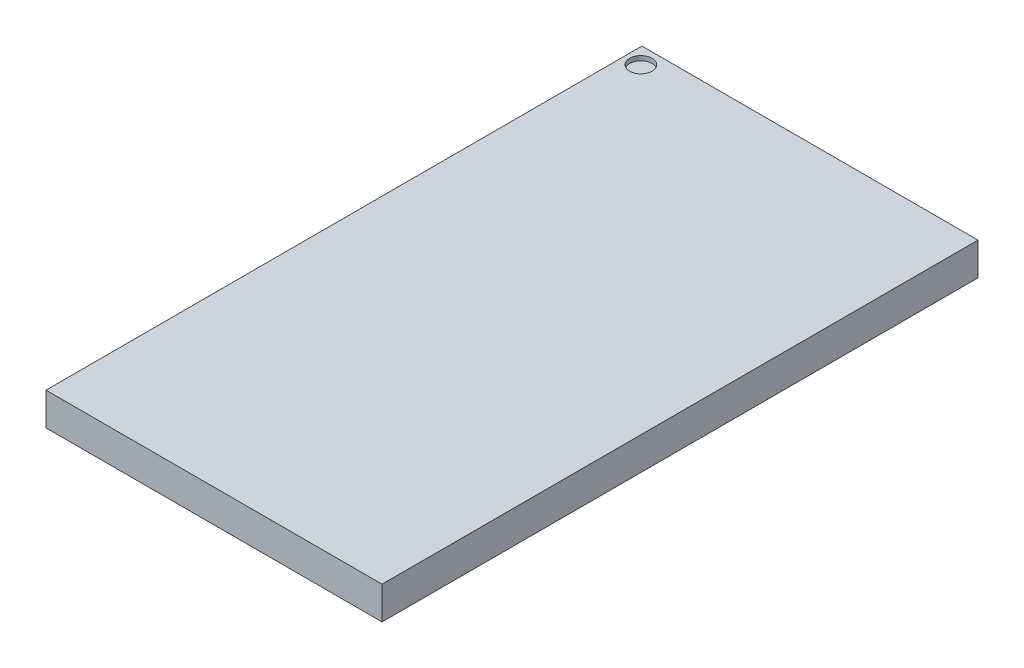
SolidWorks part; units mm, degrees
ref_plane "Front Plane" through (0, 0, 0) normal (0, 0, 1) x (1, 0, 0)
ref_plane "Top Plane" through (0, 0, 0) normal (0, 1, 0) x (1, 0, 0)
ref_plane "Right Plane" through (0, 0, 0) normal (1, 0, 0) x (0, 0, -1)
sketch "Sketch1" plane through (0, 0, 0) normal (0, 1, 0) x (1, 0, 0)
  line L1 (3.75, -6.65) -> (-3.75, -6.65)
  line L2 (3.75, -6.65) -> (3.75, 6.65)
  line L3 (3.75, 6.65) -> (-3.75, 6.65)
  line L4 (-3.75, -6.65) -> (-3.75, 6.65)
  line L5 (3.75, -6.65) -> (-3.75, 6.65) construction
  line L6 (3.75, 6.65) -> (-3.75, -6.65) construction
  point P0 (0, 0)
extrude "Boss-Extrude1" add sketch "Sketch1" along normal blind 0.73
sketch "Sketch2" plane through (0, 0.73, 0) normal (0, 1, 0) x (1, 0, 0)
  circle A0 centre (-3.401, 6.2774) radius 0.25
  point P2 (-4.8053, 5.4314)
  point P3 (-3.401, 6.2774)
  point P4 (0, 0)
extrude "Cut-Extrude1" cut sketch "Sketch2" against normal blind 0.1
sketch "Sketch3" plane through (0, 0, 0) normal (0, -1, 0) x (1, 0, 0)
  line L0 (-3.75, 6.65) -> (-3.195, 6.65) construction
  line L1 (-3.75, 6.65) -> (3.75, 6.65) construction
  line L2 (-3.75, 6.65) -> (-3.75, 6) construction
  line L3 (-3.75, -6.65) -> (-3.75, 6.65) construction
  line L4 (0, -6.65) -> (0, 6.65) construction
  line L5 (3.75, -6.65) -> (-3.75, -6.65) construction
  line L6 (3.75, 6.65) -> (3.75, 6) construction
  line L7 (3.75, 6.65) -> (3.195, 6.65) construction
  circle A0 centre (-3.195, 6) radius 0.2
  circle A1 centre (-2.395, 6) radius 0.2
  circle A2 centre (-1.595, 6) radius 0.2
  circle A3 centre (-2.395, 5.2) radius 0.2
  circle A4 centre (-1.595, 5.2) radius 0.2
  circle A5 centre (-2.395, 4.4) radius 0.2
  circle A6 centre (-1.595, 4.4) radius 0.2
  circle A7 centre (-2.395, 3.6) radius 0.2
  circle A8 centre (-1.595, 3.6) radius 0.2
  circle A9 centre (-2.395, 2.8) radius 0.2
  circle A10 centre (-1.595, 2.8) radius 0.2
  circle A11 centre (-2.395, 2) radius 0.2
  circle A12 centre (-1.595, 2) radius 0.2
  circle A13 centre (-2.395, 1.2) radius 0.2
  circle A14 centre (-1.595, 1.2) radius 0.2
  circle A15 centre (-2.395, 0.4) radius 0.2
  circle A16 centre (-1.595, 0.4) radius 0.2
  circle A17 centre (-2.395, -0.4) radius 0.2
  circle A18 centre (-1.595, -0.4) radius 0.2
  circle A19 centre (-2.395, -1.2) radius 0.2
  circle A20 centre (-1.595, -1.2) radius 0.2
  circle A21 centre (-2.395, -2) radius 0.2
  circle A22 centre (-1.595, -2) radius 0.2
  circle A23 centre (-2.395, -2.8) radius 0.2
  circle A24 centre (-1.595, -2.8) radius 0.2
  circle A25 centre (-2.395, -3.6) radius 0.2
  circle A26 centre (-1.595, -3.6) radius 0.2
  circle A27 centre (-2.395, -4.4) radius 0.2
  circle A28 centre (-1.595, -4.4) radius 0.2
  circle A29 centre (-2.395, -5.2) radius 0.2
  circle A30 centre (-1.595, -5.2) radius 0.2
  circle A31 centre (-2.395, -6) radius 0.2
  circle A32 centre (-1.595, -6) radius 0.2
  circle A33 centre (-3.195, 5.2) radius 0.2
  circle A34 centre (-3.195, 4.4) radius 0.2
  circle A35 centre (-3.195, 3.6) radius 0.2
  circle A36 centre (-3.195, 2.8) radius 0.2
  circle A37 centre (-3.195, 2) radius 0.2
  circle A38 centre (-3.195, 1.2) radius 0.2
  circle A39 centre (-3.195, 0.4) radius 0.2
  circle A40 centre (-3.195, -0.4) radius 0.2
  circle A41 centre (-3.195, -1.2) radius 0.2
  circle A42 centre (-3.195, -2) radius 0.2
  circle A43 centre (-3.195, -2.8) radius 0.2
  circle A44 centre (-3.195, -3.6) radius 0.2
  circle A45 centre (-3.195, -4.4) radius 0.2
  circle A46 centre (-3.195, -5.2) radius 0.2
  circle A47 centre (-3.195, -6) radius 0.2
  circle A48 centre (3.195, -6) radius 0.2
  circle A49 centre (3.195, -5.2) radius 0.2
  circle A50 centre (3.195, -4.4) radius 0.2
  circle A51 centre (3.195, -3.6) radius 0.2
  circle A52 centre (3.195, -2.8) radius 0.2
  circle A53 centre (3.195, -2) radius 0.2
  circle A54 centre (3.195, -1.2) radius 0.2
  circle A55 centre (3.195, -0.4) radius 0.2
  circle A56 centre (3.195, 0.4) radius 0.2
  circle A57 centre (3.195, 1.2) radius 0.2
  circle A58 centre (3.195, 2) radius 0.2
  circle A59 centre (3.195, 2.8) radius 0.2
  circle A60 centre (3.195, 3.6) radius 0.2
  circle A61 centre (3.195, 4.4) radius 0.2
  circle A62 centre (3.195, 5.2) radius 0.2
  circle A63 centre (1.595, -6) radius 0.2
  circle A64 centre (2.395, -6) radius 0.2
  circle A65 centre (1.595, -5.2) radius 0.2
  circle A66 centre (2.395, -5.2) radius 0.2
  circle A67 centre (1.595, -4.4) radius 0.2
  circle A68 centre (2.395, -4.4) radius 0.2
  circle A69 centre (1.595, -3.6) radius 0.2
  circle A70 centre (2.395, -3.6) radius 0.2
  circle A71 centre (1.595, -2.8) radius 0.2
  circle A72 centre (2.395, -2.8) radius 0.2
  circle A73 centre (1.595, -2) radius 0.2
  circle A74 centre (2.395, -2) radius 0.2
  circle A75 centre (1.595, -1.2) radius 0.2
  circle A76 centre (2.395, -1.2) radius 0.2
  circle A77 centre (1.595, -0.4) radius 0.2
  circle A78 centre (2.395, -0.4) radius 0.2
  circle A79 centre (1.595, 0.4) radius 0.2
  circle A80 centre (2.395, 0.4) radius 0.2
  circle A81 centre (1.595, 1.2) radius 0.2
  circle A82 centre (2.395, 1.2) radius 0.2
  circle A83 centre (1.595, 2) radius 0.2
  circle A84 centre (2.395, 2) radius 0.2
  circle A85 centre (1.595, 2.8) radius 0.2
  circle A86 centre (2.395, 2.8) radius 0.2
  circle A87 centre (1.595, 3.6) radius 0.2
  circle A88 centre (2.395, 3.6) radius 0.2
  circle A89 centre (1.595, 4.4) radius 0.2
  circle A90 centre (2.395, 4.4) radius 0.2
  circle A91 centre (1.595, 5.2) radius 0.2
  circle A92 centre (2.395, 5.2) radius 0.2
  circle A93 centre (1.595, 6) radius 0.2
  circle A94 centre (2.395, 6) radius 0.2
  circle A95 centre (3.195, 6) radius 0.2
  dimension "D1" = 3
  dimension "D2" = 16
extrude "Boss-Extrude2" add sketch "Sketch3" along normal blind 0.3
fillet "Fillet1" radius 0.15 96 edges at (3.195, -0.3, 6.2) (2.395, -0.3, 6.2) (1.595, -0.3, 6.2) (2.395, -0.3, 5.4) (1.595, -0.3, 5.4) (2.395, -0.3, 4.6) (1.595, -0.3, 4.6) (2.395, -0.3, 3.8) (1.595, -0.3, 3.8) (2.395, -0.3, 3) (1.595, -0.3, 3) (2.395, -0.3, 2.2) (1.595, -0.3, 2.2) (2.395, -0.3, 1.4) (1.595, -0.3, 1.4) (2.395, -0.3, 0.6) (1.595, -0.3, 0.6) (2.395, -0.3, -0.2) (1.595, -0.3, -0.2) (2.395, -0.3, -1) (1.595, -0.3, -1) (2.395, -0.3, -1.8) (1.595, -0.3, -1.8) (2.395, -0.3, -2.6) (1.595, -0.3, -2.6) (2.395, -0.3, -3.4) (1.595, -0.3, -3.4) (2.395, -0.3, -4.2) (1.595, -0.3, -4.2) (2.395, -0.3, -5) (1.595, -0.3, -5) (2.395, -0.3, -5.8) (1.595, -0.3, -5.8) (3.195, -0.3, 5.4) (3.195, -0.3, 4.6) (3.195, -0.3, 3.8) (3.195, -0.3, 3) (3.195, -0.3, 2.2) (3.195, -0.3, 1.4) (3.195, -0.3, 0.6) (3.195, -0.3, -0.2) (3.195, -0.3, -1) (3.195, -0.3, -1.8) (3.195, -0.3, -2.6) (3.195, -0.3, -3.4) (3.195, -0.3, -4.2) (3.195, -0.3, -5) (3.195, -0.3, -5.8) (-3.195, -0.3, -6.2) (-3.195, -0.3, -5.4) (-3.195, -0.3, -4.6) (-3.195, -0.3, -3.8) (-3.195, -0.3, -3) (-3.195, -0.3, -2.2) (-3.195, -0.3, -1.4) (-3.195, -0.3, -0.6) (-3.195, -0.3, 0.2) (-3.195, -0.3, 1) (-3.195, -0.3, 1.8) (-3.195, -0.3, 2.6) (-3.195, -0.3, 3.4) (-3.195, -0.3, 4.2) (-3.195, -0.3, 5) (-1.595, -0.3, -6.2) (-2.395, -0.3, -6.2) (-1.595, -0.3, -5.4) (-2.395, -0.3, -5.4) (-1.595, -0.3, -4.6) (-2.395, -0.3, -4.6) (-1.595, -0.3, -3.8) (-2.395, -0.3, -3.8) (-1.595, -0.3, -3) (-2.395, -0.3, -3) (-1.595, -0.3, -2.2) (-2.395, -0.3, -2.2) (-1.595, -0.3, -1.4) (-2.395, -0.3, -1.4) (-1.595, -0.3, -0.6) (-2.395, -0.3, -0.6) (-1.595, -0.3, 0.2) (-2.395, -0.3, 0.2) (-1.595, -0.3, 1) (-2.395, -0.3, 1) (-1.595, -0.3, 1.8) (-2.395, -0.3, 1.8) (-1.595, -0.3, 2.6) (-2.395, -0.3, 2.6) (-1.595, -0.3, 3.4) (-2.395, -0.3, 3.4) (-1.595, -0.3, 4.2) (-2.395, -0.3, 4.2) (-1.595, -0.3, 5) (-2.395, -0.3, 5) (-1.595, -0.3, 5.8) (-2.395, -0.3, 5.8) (-3.195, -0.3, 5.8)
